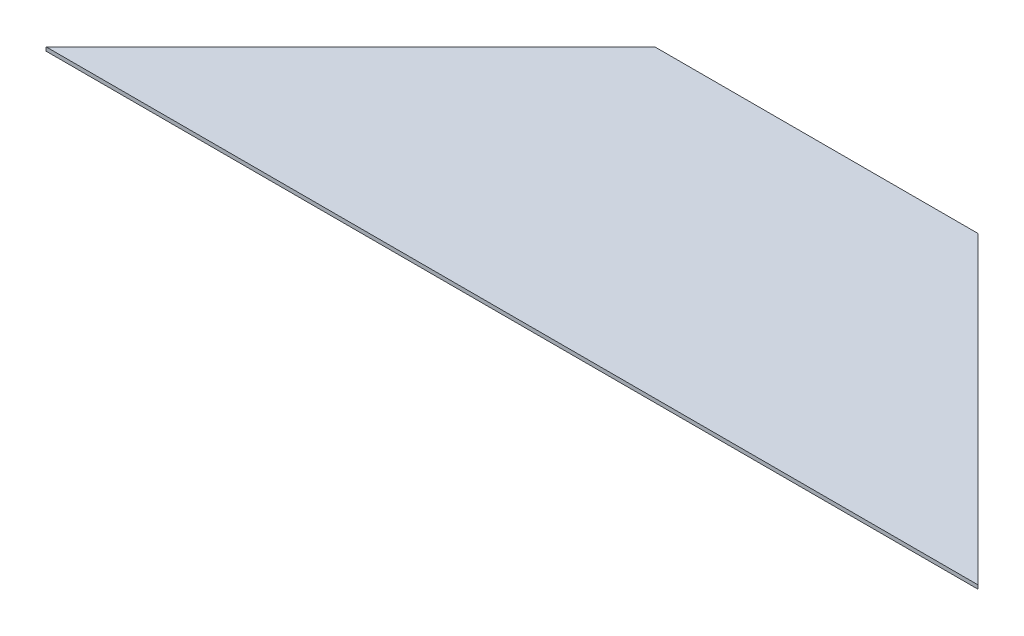
SolidWorks part; units mm, degrees
ref_plane "前视基准面" through (0, 0, 0) normal (0, 0, 1) x (1, 0, 0)
ref_plane "上视基准面" through (0, 0, 0) normal (0, 1, 0) x (1, 0, 0)
ref_plane "右视基准面" through (0, 0, 0) normal (1, 0, 0) x (0, 0, -1)
sketch "草图1" plane through (0, 0, 0) normal (0, 1, 0) x (1, 0, 0)
  line L0 (0, 0) -> (490, 0)
  line L1 (490, 0) -> (330, 160)
  line L2 (330, 160) -> (160, 160)
  line L3 (160, 160) -> (0, 0)
  dimension "D1" = 490
  dimension "D2" = 45
  dimension "D3" = 45
  dimension "D4" = 160
extrude "凸台-拉伸1" add sketch "草图1" along normal blind 2
